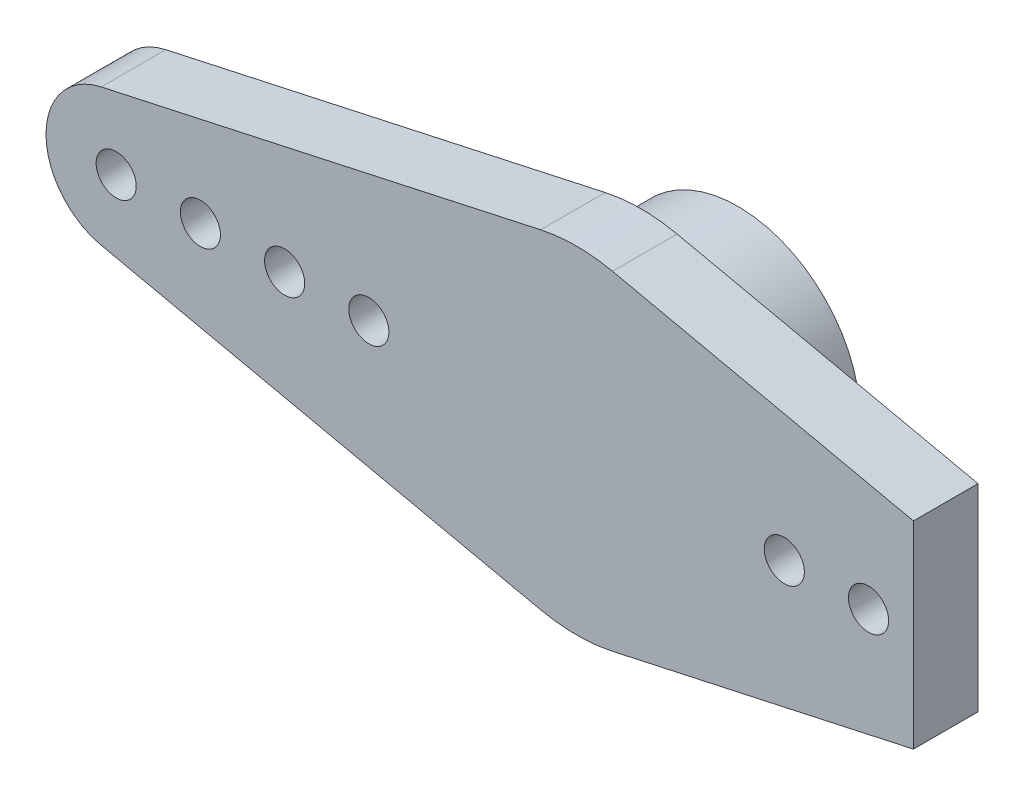
SolidWorks part; units mm, degrees
ref_plane "前视基准面" through (0, 0, 0) normal (0, 0, 1) x (1, 0, 0)
ref_plane "上视基准面" through (0, 0, 0) normal (0, 1, 0) x (1, 0, 0)
ref_plane "右视基准面" through (0, 0, 0) normal (1, 0, 0) x (0, 0, -1)
sketch "草图1" plane through (0, 0, 0) normal (0, 0, 1) x (1, 0, 0)
  circle A0 centre (0, 0) radius 4.35
  dimension "D1" = 8.7
extrude "凸台-拉伸1" add sketch "草图1" along normal blind 3.45
sketch "草图2" plane through (0, 0, 3.45) normal (0, 0, 1) x (1, 0, 0)
  line L0 (-1.2805, 5.8618) -> (-16.9335, 2.4424)
  line L1 (-1.2805, -5.8618) -> (-16.9335, -2.4424)
  line L2 (0, 0) -> (-31.8332, 0) construction
  line L3 (0, 0) -> (0, 9.7252) construction
  line L4 (1.2805, -5.8618) -> (16.9335, -2.4424)
  line L5 (1.2805, 5.8618) -> (16.9335, 2.4424)
  arc A0 (-1.2805, -5.8618) -> (1.2805, -5.8618) centre (0, 0) ccw
  arc A1 (-16.9335, 2.4424) -> (-16.9335, -2.4424) centre (-16.4, 0) ccw
  arc A2 (16.9335, 2.4424) -> (16.9335, -2.4424) centre (16.4, 0) cw
  arc A3 (1.2805, 5.8618) -> (-1.2805, 5.8618) centre (0, 0) ccw
  circle A4 centre (-16.4, 0) radius 0.715
  circle A5 centre (-13.4, 0) radius 0.715
  circle A6 centre (-10.4, 0) radius 0.715
  circle A7 centre (-7.4, 0) radius 0.715
  circle A8 centre (7.4, 0) radius 0.715
  circle A9 centre (10.4, 0) radius 0.715
  circle A10 centre (13.4, 0) radius 0.715
  circle A11 centre (16.4, 0) radius 0.715
  dimension "D2" = 12
  dimension "D3" = 2.5
  dimension "D4" = 1.43
  dimension "D1" = 32.8
  dimension "D5" = 4
extrude "凸台-拉伸2" add sketch "草图2" along normal blind 2.3
sketch "草图3" plane through (0, 0, 0) normal (0, 0, -1) x (-1, 0, 0)
  circle A0 centre (0, 0) radius 2.85
  dimension "D1" = 5.7
extrude "切除-拉伸1" cut sketch "草图3" against normal blind 3.4
sketch "草图4" plane through (0, 0, 5.75) normal (0, 0, 1) x (1, 0, 0)
  line L1 (24.9039, -5.8564) -> (12, -5.8564)
  line L2 (24.9039, -5.8564) -> (24.9039, 4.705)
  line L3 (24.9039, 4.705) -> (12, 4.705)
  line L4 (12, -5.8564) -> (12, 4.705)
  dimension "D1" = 12
extrude "切除-拉伸2" cut sketch "草图4" against normal blind 10
